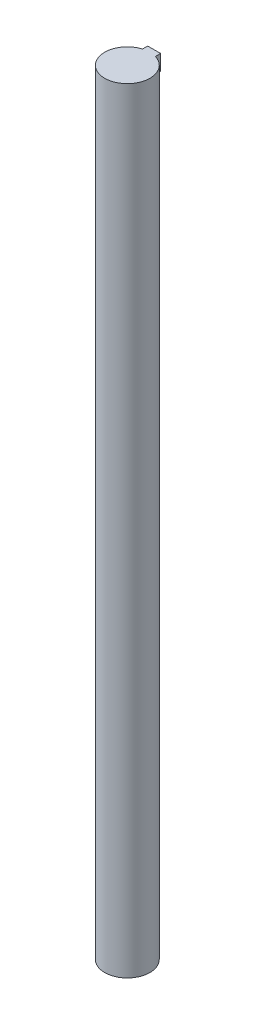
SolidWorks part; units mm, degrees
ref_plane "Front Plane" through (0, 0, 0) normal (0, 0, 1) x (1, 0, 0)
ref_plane "Top Plane" through (0, 0, 0) normal (0, 1, 0) x (1, 0, 0)
ref_plane "Right Plane" through (0, 0, 0) normal (1, 0, 0) x (0, 0, -1)
sketch "Sketch1" plane through (0, 0, 0) normal (0, 1, 0) x (1, 0, 0)
  circle A0 centre (0, 0) radius 17.5
extrude "Boss-Extrude1" add sketch "Sketch1" along normal blind 600
sketch "Sketch5" plane through (0, 600, 0) normal (0, 1, 0) x (1, 0, 0)
  line L0 (0, 0) -> (0, 24.7624) construction
  line L10 (-5, 16.7705) -> (5, 16.7705)
  line L11 (-5, 16.7705) -> (-5, 20.8005)
  line L12 (-5, 20.8005) -> (5, 20.8005)
  line L13 (5, 16.7705) -> (5, 20.8005)
  line L14 (-5, 16.7705) -> (5, 20.8005) construction
  line L15 (-5, 20.8005) -> (5, 16.7705) construction
  point P0 (0, 18.7855)
  dimension "D1" = 16.7705
  dimension "D2" = 10
  dimension "D3" = 4.03
extrude "Boss-Extrude2" add sketch "Sketch5" against normal blind 12
sketch "Sketch2" plane through (0, 600, 0) normal (0, 1, 0) x (1, 0, 0)
